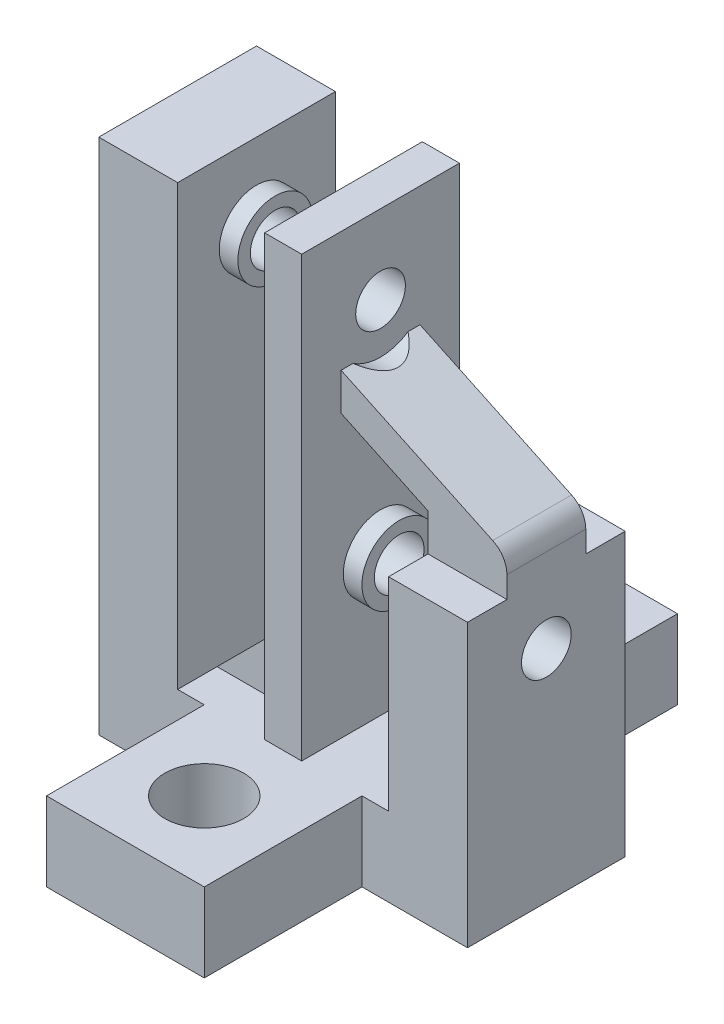
SolidWorks part; units mm, degrees
ref_plane "Front Plane" through (0, 0, 0) normal (0, 0, 1) x (1, 0, 0)
ref_plane "Top Plane" through (0, 0, 0) normal (0, 1, 0) x (1, 0, 0)
ref_plane "Right Plane" through (0, 0, 0) normal (1, 0, 0) x (0, 0, -1)
sketch "Sketch1" plane through (0, 0, 0) normal (0, 0, 1) x (1, 0, 0)
  line L1 (1.4925, 20.8434) -> (-1.4925, 20.8434)
  line L2 (1.4925, 20.8434) -> (1.4925, -20.8434)
  line L3 (1.4925, -20.8434) -> (-1.4925, -20.8434)
  line L4 (-1.4925, 20.8434) -> (-1.4925, -20.8434)
  line L5 (1.4925, 20.8434) -> (-1.4925, -20.8434) construction
  line L6 (1.4925, -20.8434) -> (-1.4925, 20.8434) construction
  point P0 (0, 0)
  dimension "D3" = 2.985
  dimension "D4" = 41.6868
extrude "Boss-Extrude1" add sketch "Sketch1" along normal blind 12.7
sketch "Sketch5" plane through (1.4925, 0, 0) normal (1, 0, 0) x (0, 0, -1)
  line L0 (-12.7, 20.8434) -> (0, 20.8434) construction
  circle A0 centre (-6.35, 14.4934) radius 2
  point P5 (-6.35, 20.8434)
  dimension "D2" = 4
  dimension "D1" = 6.35
extrude "Cut-Extrude2" cut sketch "Sketch5" against normal through all
sketch "Sketch8" plane through (0, 0, 12.7) normal (0, 0, 1) x (1, 0, 0)
  line L0 (1.4925, -20.8434) -> (-1.4925, -20.8434) construction
  line L1 (-6.35, -20.8434) -> (6.35, -20.8434)
  line L2 (-6.35, -20.8434) -> (-6.35, -14.4934)
  line L3 (-6.35, -14.4934) -> (6.35, -14.4934)
  line L4 (6.35, -20.8434) -> (6.35, -14.4934)
  point P5 (0, -14.4934)
  dimension "D1" = 6.35
  dimension "D2" = 12.7
extrude "Boss-Extrude2" add sketch "Sketch8" along normal blind 12.7
sketch "Sketch9" plane through (0, -14.4934, 0) normal (0, 1, 0) x (1, 0, 0)
  line L0 (-6.35, -19.05) -> (6.35, -19.05) construction
  line L1 (-6.35, -25.4) -> (-6.35, -12.7) construction
  line L2 (6.35, -25.4) -> (6.35, -12.7) construction
  circle A0 centre (0, -19.05) radius 3.175
  point P9 (0, -19.05)
  dimension "D1" = 6.35
extrude "Cut-Extrude3" cut sketch "Sketch9" against normal blind 12.7
sketch "Sketch10" plane through (0, 20.8434, 0) normal (0, 1, 0) x (1, 0, 0)
  line L0 (0, -12.7) -> (0, 0) construction
  line L1 (1.4925, -12.7) -> (-1.4925, -12.7) construction
ref_plane "Plane1" through (0, 0, 6.35) normal (0, 0, -1) x (-1, 0, 0)
mirror "Mirror1" about plane through (0, 0, 6.35) normal (0, 0, -1) of "Boss-Extrude2", "Cut-Extrude3"
sketch "Sketch11" plane through (0, 0, 12.7) normal (0, 0, -1) x (-1, 0, 0)
  line L1 (-6.35, -14.4934) -> (6.35, -14.4934)
  line L2 (-6.35, -14.4934) -> (-6.35, -20.8434)
  line L3 (-6.35, -20.8434) -> (6.35, -20.8434)
  line L4 (6.35, -14.4934) -> (6.35, -20.8434)
extrude "Boss-Extrude3" add sketch "Sketch11" along normal up to surface (12.7 mm away) up to face at (-3.9212, -17.6684, 0)
sketch "Sketch12" plane through (1.4925, 0, 0) normal (1, 0, 0) x (0, 0, -1)
  line L0 (-6.35, -19.4352) -> (-6.35, 19.4352) construction
  circle A0 centre (-6.35, -3.1444) radius 2
  circle A1 centre (-6.35, 14.4934) radius 2 construction
  dimension "D1" = 4
  dimension "D2" = 17.6378
extrude "Cut-Extrude4" cut sketch "Sketch12" against normal up to next
sketch "Sketch15" plane through (-1.4925, 0, 0) normal (-1, 0, 0) x (0, 0, 1)
  circle A0 centre (6.35, 14.4934) radius 3
  circle A1 centre (6.35, 14.4934) radius 2
  circle A2 centre (6.35, 14.4934) radius 2 construction
  dimension "D1" = 1
extrude "Boss-Extrude5" add sketch "Sketch15" along normal blind 1.5
sketch "Sketch16" plane through (1.4925, 0, 0) normal (1, 0, 0) x (0, 0, -1)
  circle A0 centre (-6.35, -3.1444) radius 3
  circle A1 centre (-6.35, -3.1444) radius 2
  circle A2 centre (-6.35, -3.1444) radius 2 construction
  dimension "D1" = 1
extrude "Boss-Extrude6" add sketch "Sketch16" along normal blind 1.5
sketch "Sketch13" plane through (0, 0, 6.35) normal (0, 0, -1) x (-1, 0, 0)
  line L5 (-1.4925, 20.8434) -> (1.4925, 20.8434) construction
  line L7 (-14.8425, -20.8434) -> (-14.8425, 20.8434)
  line L8 (-14.8425, 20.8434) -> (-8.4925, 20.8434)
  line L9 (-8.4925, -20.8434) -> (-8.4925, 20.8434)
  line L11 (-14.8425, -20.8434) -> (-8.4925, -20.8434)
  line L12 (6.35, -20.8434) -> (-6.35, -20.8434) construction
  line L14 (8.4925, 20.8434) -> (14.8425, 20.8434)
  line L15 (8.4925, 20.8434) -> (8.4925, -20.8434)
  line L16 (8.4925, -20.8434) -> (14.8425, -20.8434)
  line L17 (14.8425, 20.8434) -> (14.8425, -20.8434)
  line L18 (-2.9925, -0.1444) -> (-2.9925, -6.1444) construction
  line L19 (2.9925, 11.4934) -> (2.9925, 17.4934) construction
  line L20 (-8.4925, -20.8434) -> (-1.4925, -20.8434)
  line L21 (-8.4925, -20.8434) -> (-8.4925, -14.4934)
  line L22 (-8.4925, -14.4934) -> (-1.4925, -14.4934)
  line L23 (-1.4925, -20.8434) -> (-1.4925, -14.4934)
  line L25 (8.4925, -20.8434) -> (1.4925, -20.8434)
  line L26 (8.4925, -20.8434) -> (8.4925, -14.4934)
  line L27 (8.4925, -14.4934) -> (1.4925, -14.4934)
  line L28 (1.4925, -20.8434) -> (1.4925, -14.4934)
  dimension "D1" = 5.5
  dimension "D2" = 6.35
  dimension "D3" = 5.5
extrude "Boss-Extrude4" add sketch "Sketch13" along normal mid plane 12.7 contours L7 L11 L9 L8 | L20 L23 L22 L9 | L17 L14 L15 L16 | L28 L25 L15 L27
sketch "Sketch17" plane through (-14.8425, 0, 0) normal (-1, 0, 0) x (0, 0, 1)
  line L0 (0, 18.8775) -> (12.7, 18.8775) construction
  line L1 (0, 20.8434) -> (0, -20.8434) construction
  line L2 (12.7, 20.8434) -> (12.7, -20.8434) construction
  circle A0 centre (6.35, 14.4934) radius 2
  circle A1 centre (6.35, -3.1444) radius 2
  circle A2 centre (6.35, 14.4934) radius 2 construction
  circle A3 centre (6.35, -3.1444) radius 2 construction
  point P4 (0, 0)
  point P11 (6.35, 18.8775)
extrude "Cut-Extrude5" cut sketch "Sketch17" against normal up to surface (29.685 mm away) up to face at (14.8425, 0, 6.35)
sketch "Sketch18" plane through (8.4925, 0, 0) normal (-1, 0, 0) x (0, 0, 1)
  circle A0 centre (6.35, -3.1444) radius 3
  circle A1 centre (6.35, -3.1444) radius 2
  circle A2 centre (6.35, -3.1444) radius 2 construction
  dimension "D1" = 1
extrude "Boss-Extrude7" add sketch "Sketch18" along normal blind 1.5
sketch "Sketch19" plane through (-8.4925, 0, 0) normal (1, 0, 0) x (0, 0, -1)
  circle A0 centre (-6.35, 14.4934) radius 3
  circle A1 centre (-6.35, 14.4934) radius 2
  circle A2 centre (-6.35, 14.4934) radius 2 construction
  dimension "D1" = 1
extrude "Boss-Extrude8" add sketch "Sketch19" along normal blind 1.5
sketch "Sketch20" plane through (0, 0, 0) normal (0, 0, -1) x (-1, 0, 0)
  line L0 (-8.4925, -14.4934) -> (-8.4925, 20.8434) construction
  line L1 (-14.8425, 20.8434) -> (-8.4925, 20.8434)
  line L2 (-14.8425, 20.8434) -> (-14.8425, 1.8556)
  line L3 (-14.8425, 1.8556) -> (-8.4925, 1.8556)
  line L4 (-8.4925, 20.8434) -> (-8.4925, 1.8556)
  line L5 (-6.9925, -0.1444) -> (-8.4925, -0.1444) construction
  dimension "D1" = 2
extrude "Cut-Extrude6" cut sketch "Sketch20" against normal up to next
sketch "Sketch21" plane through (-14.8425, 0, 0) normal (-1, 0, 0) x (0, 0, 1)
  circle A0 centre (6.35, -3.1444) radius 2
  circle A1 centre (6.35, -3.1444) radius 2 construction
extrude "Boss-Extrude9" add sketch "Sketch21" against normal up to surface (6.35 mm away) up to face at (-8.4925, 3.175, 6.35)
sketch "Sketch22" plane through (0, 0, 6.35) normal (0, 0, 1) x (1, 0, 0)
  line L0 (8.4925, -14.4934) -> (8.4925, 1.8556) construction
  line L1 (14.8425, 1.8556) -> (8.4925, 1.8556)
  line L2 (14.8425, 1.8556) -> (14.8425, 4.8556)
  line L3 (14.8425, 4.8556) -> (8.4925, 4.8556)
  line L4 (8.4925, 1.8556) -> (8.4925, 4.8556)
  line L10 (8.4925, 4.8556) -> (1.4925, 8.1627)
  line L11 (1.4925, 20.8434) -> (1.4925, -14.4934) construction
  line L12 (1.4925, 8.1627) -> (1.4925, 11.1627)
  line L13 (1.4925, 11.1627) -> (14.8425, 4.8556)
  point P7 (1.4925, 9.8968)
  point P12 (1.4925, 8.0254)
  point P13 (1.4925, 10.6478)
  dimension "D1" = 3
  dimension "D2" = 3
extrude "Boss-Extrude10" add sketch "Sketch22" against normal mid plane 6.35
sketch "Sketch23" plane through (0, 0, 6.35) normal (0, 0, -1) x (-1, 0, 0)
  line L0 (1.4925, -7.4934) -> (8.4925, -14.4934)
  line L1 (1.4925, 20.8434) -> (1.4925, -14.4934) construction
  line L2 (8.4925, -14.4934) -> (1.4925, -14.4934)
  line L3 (-6.35, -14.4934) -> (6.35, -14.4934) construction
  line L4 (1.4925, -14.4934) -> (1.4925, -7.4934)
extrude "Boss-Extrude11" add sketch "Sketch23" along normal mid plane 6.35
sketch "Sketch24" plane through (1.4925, 0, 0) normal (1, 0, 0) x (0, 0, -1)
  circle A0 centre (-6.35, 14.4934) radius 4
  dimension "D1" = 8
extrude "Cut-Extrude8" cut sketch "Sketch24" along normal blind 6.35
fillet "Fillet3" radius 2 1 edges at (14.8425, 4.8556, 6.35)
